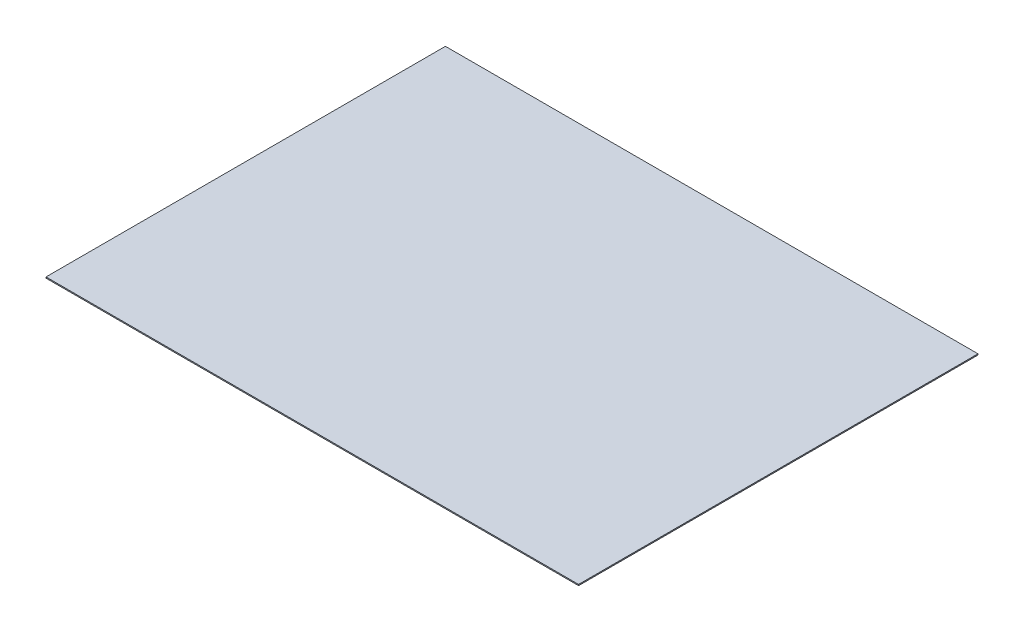
SolidWorks part; units mm, degrees
ref_plane "Front Plane" through (0, 0, 0) normal (0, 0, 1) x (1, 0, 0)
ref_plane "Top Plane" through (0, 0, 0) normal (0, 1, 0) x (1, 0, 0)
ref_plane "Right Plane" through (0, 0, 0) normal (1, 0, 0) x (0, 0, -1)
sketch "Sketch1" plane through (0, 0, 0) normal (0, 1, 0) x (1, 0, 0)
  line L1 (0, 0) -> (1219.2, 0)
  line L2 (0, 0) -> (0, 914.4)
  line L3 (0, 914.4) -> (1219.2, 914.4)
  line L4 (1219.2, 0) -> (1219.2, 914.4)
  dimension "D1" = 914.4
  dimension "D2" = 1219.2
extrude "Boss-Extrude1" add sketch "Sketch1" along normal blind 2.54
